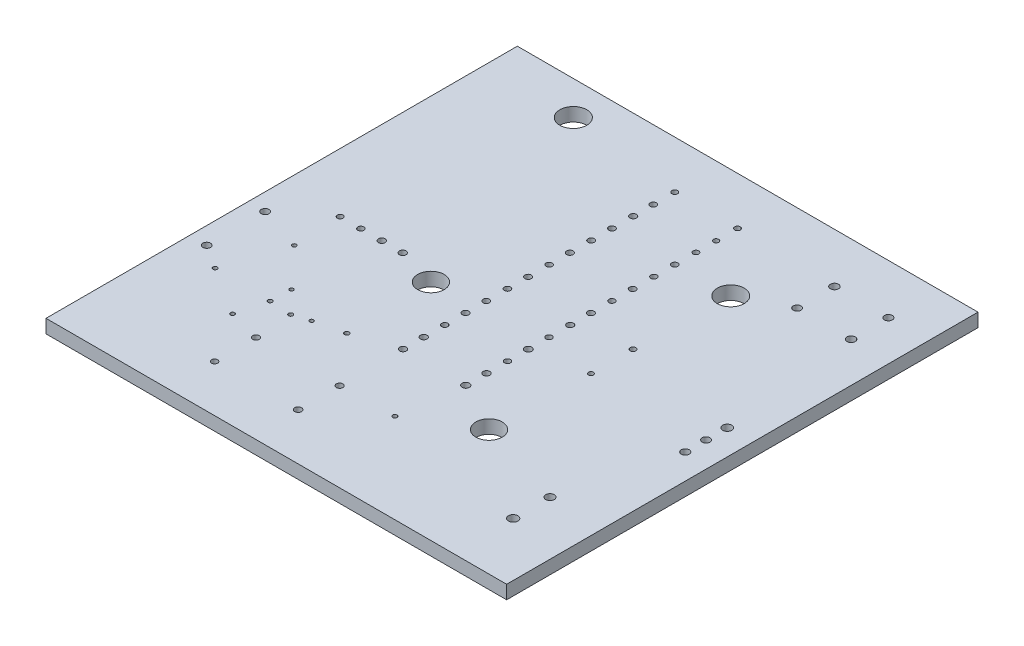
SolidWorks part; units mm, degrees
ref_plane "Front Plane" through (0, 0, 0) normal (0, 0, 1) x (1, 0, 0)
ref_plane "Top Plane" through (0, 0, 0) normal (0, 1, 0) x (1, 0, 0)
ref_plane "Right Plane" through (0, 0, 0) normal (1, 0, 0) x (0, 0, -1)
sketch "Sketch1" plane through (0, 0, 0) normal (0, 1, 0) x (1, 0, 0)
  line L1 (-27.305, -27.94) -> (27.305, -27.94)
  line L2 (-27.305, -27.94) -> (-27.305, 27.94)
  line L3 (-27.305, 27.94) -> (27.305, 27.94)
  line L4 (27.305, -27.94) -> (27.305, 27.94)
  line L5 (-27.305, -27.94) -> (27.305, 27.94) construction
  line L6 (-27.305, 27.94) -> (27.305, -27.94) construction
  point P0 (0, 0)
  dimension "D1" = 55.88
  dimension "D2" = 54.61
extrude "Boss-Extrude1" add sketch "Sketch1" along normal blind 1.6
sketch "Sketch2" plane through (0, 1.6, 0) normal (0, 1, 0) x (1, 0, 0)
  circle A0 centre (-16.6643, 23.932) radius 1.5994
  circle A1 centre (10.9803, 14.9509) radius 1.5931
  circle A2 centre (16.1667, 17.6326) radius 0.4526
  circle A3 centre (16.1667, 22.0601) radius 0.48
  circle A4 centre (22.5675, 22.0601) radius 0.4651
  circle A5 centre (22.5675, 17.6326) radius 0.4866
  circle A6 centre (-8.2131, -1.3991) radius 1.5659
  circle A7 centre (-12.8808, -0.0683) radius 0.3979
  circle A8 centre (-15.3678, -0.0683) radius 0.3979
  circle A9 centre (-17.8547, -0.0683) radius 0.3566
  circle A10 centre (-20.3124, -0.0683) radius 0.3336
  circle A11 centre (-20.0759, -5.7385) radius 0.2395
  circle A12 centre (-15.7046, -10.4281) radius 0.2262
  circle A13 centre (-11.3071, -12.4585) radius 0.2333
  circle A14 centre (-13.1901, -13.0477) radius 0.2562
  circle A15 centre (-15.7844, -12.8838) radius 0.2554
  circle A16 centre (-22.4311, -12.7656) radius 0.2481
  circle A17 centre (-25.2756, -10.917) radius 0.4477
  circle A18 centre (-25.2756, -3.992) radius 0.4523
  circle A19 centre (-16.7059, -16.4215) radius 0.2399
  circle A20 centre (-12.8808, -17.4593) radius 0.3915
  circle A21 centre (-12.8808, -22.3758) radius 0.3603
  circle A22 centre (-2.9834, -22.3758) radius 0.4045
  circle A23 centre (-2.9834, -17.4593) radius 0.3848
  circle A24 centre (3.4278, -17.3194) radius 0.2571
  circle A25 centre (-7.9328, -11.6448) radius 0.2733
  circle A26 centre (-2.9834, -9.9355) radius 0.3965
  circle A27 centre (-2.9834, -7.4806) radius 0.3934
  circle A28 centre (-2.9834, -4.9878) radius 0.3556
  circle A29 centre (-2.9834, -2.5214) radius 0.3775
  circle A30 centre (-2.9834, -0.0683) radius 0.3778
  circle A31 centre (-2.9834, 2.4447) radius 0.3633
  circle A32 centre (-2.9834, 4.8931) radius 0.3786
  circle A33 centre (-2.9834, 7.3856) radius 0.3553
  circle A34 centre (-2.9834, 9.8492) radius 0.383
  circle A35 centre (-2.9834, 12.3631) radius 0.3697
  circle A36 centre (-2.9834, 14.8339) radius 0.3712
  circle A37 centre (-2.9834, 17.348) radius 0.3859
  circle A38 centre (-2.9834, 19.7372) radius 0.3639
  circle A39 centre (-2.9834, 22.2772) radius 0.3335
  circle A40 centre (4.4569, 19.7372) radius 0.31
  circle A41 centre (4.4569, 22.2772) radius 0.3339
  circle A42 centre (4.4569, 17.348) radius 0.3303
  circle A43 centre (4.4569, 14.8339) radius 0.3644
  circle A44 centre (4.4569, 12.3631) radius 0.3538
  circle A45 centre (4.4569, 9.8492) radius 0.3729
  circle A46 centre (4.4569, 7.3856) radius 0.3486
  circle A47 centre (4.4569, 4.8931) radius 0.3848
  circle A48 centre (4.4569, 2.4447) radius 0.3876
  circle A49 centre (4.4569, -0.0683) radius 0.3545
  circle A50 centre (4.4569, -2.5214) radius 0.4159
  circle A51 centre (4.4569, -4.9878) radius 0.3515
  circle A52 centre (4.4569, -7.4806) radius 0.3924
  circle A53 centre (4.4569, -9.9355) radius 0.4343
  circle A54 centre (10.6697, -1.3048) radius 0.2926
  circle A55 centre (10.6697, 3.6823) radius 0.3355
  circle A56 centre (10.3771, -13.1011) radius 1.5642
  circle A57 centre (20.9291, -16.4215) radius 0.5086
  circle A58 centre (20.9291, -20.7898) radius 0.5556
  circle A59 centre (24.3096, 1.2066) radius 0.5301
  circle A60 centre (24.3096, -1.3048) radius 0.4596
  circle A61 centre (24.3096, -3.7708) radius 0.4653
extrude "Cut-Extrude1" cut sketch "Sketch2" against normal through all
